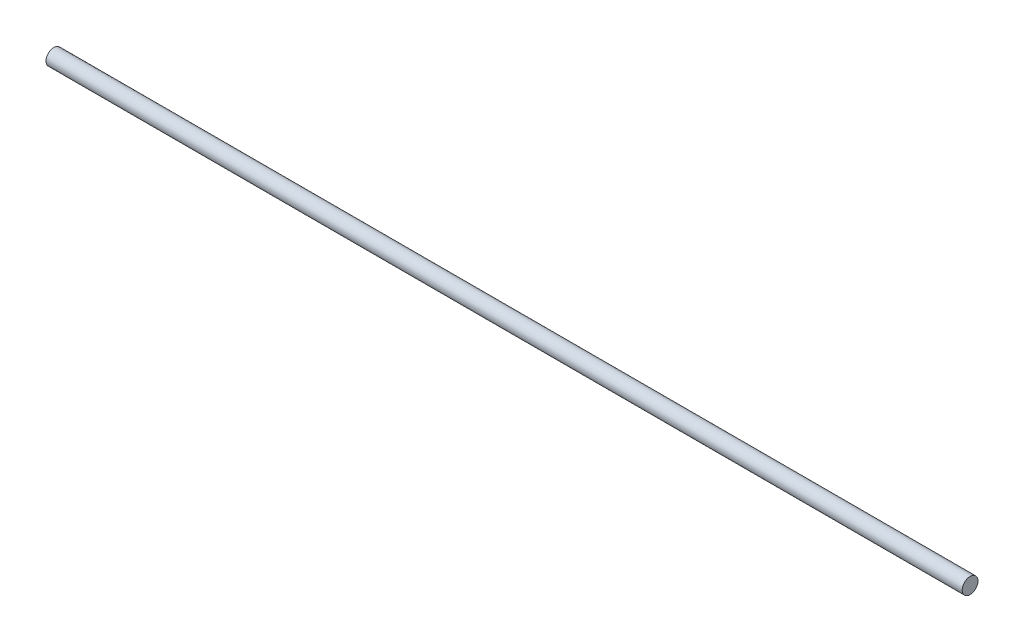
SolidWorks part; units mm, degrees
ref_plane "Front Plane" through (0, 0, 0) normal (0, 0, 1) x (1, 0, 0)
ref_plane "Top Plane" through (0, 0, 0) normal (0, 1, 0) x (1, 0, 0)
ref_plane "Right Plane" through (0, 0, 0) normal (1, 0, 0) x (0, 0, -1)
sketch "Sketch1" plane through (0, 0, 0) normal (1, 0, 0) x (0, 0, -1)
  circle A0 centre (0, 0) radius 5
  dimension "D1" = 10
extrude "Boss-Extrude1" add sketch "Sketch1" along normal blind 580
